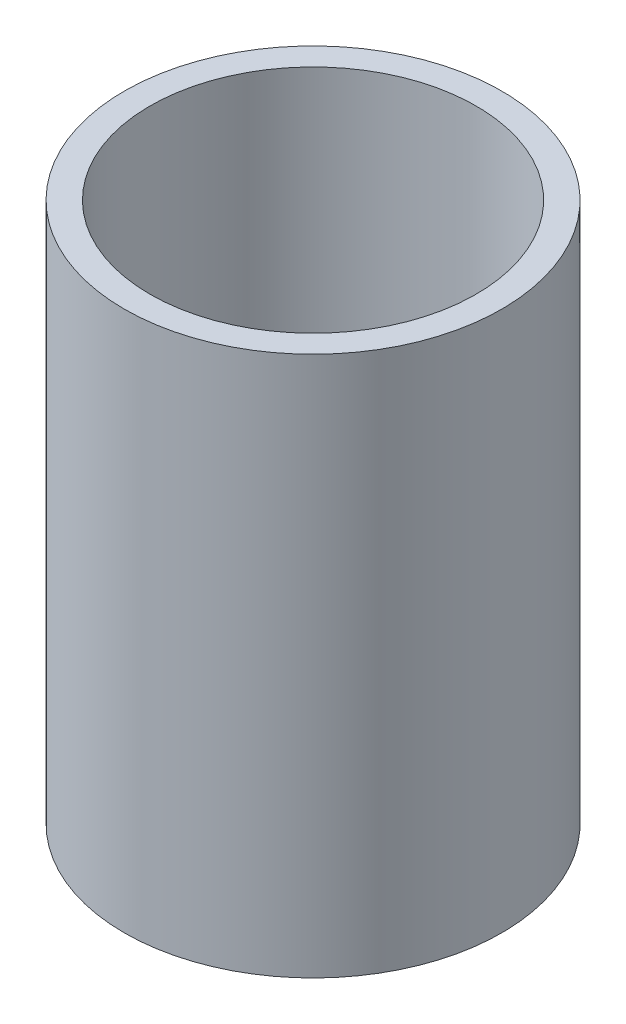
SolidWorks part; units mm, degrees
material "Corrugated Paper"
ref_plane "Front Plane" through (0, 0, 0) normal (0, 0, 1) x (1, 0, 0)
ref_plane "Top Plane" through (0, 0, 0) normal (0, 1, 0) x (1, 0, 0)
ref_plane "Right Plane" through (0, 0, 0) normal (1, 0, 0) x (0, 0, -1)
ref_axis "Axis1" through (0, 55, 0) along (0, -1, 0)
sketch "Sketch1" plane through (0, 0, 0) normal (0, 0, 1) x (1, 0, 0)
  line L1 (-46.609, 45.6176) -> (-40.259, 45.6176)
  line L2 (-46.609, 45.6176) -> (-46.609, -87.7324)
  line L3 (-46.609, -87.7324) -> (-40.259, -87.7324)
  line L4 (-40.259, 45.6176) -> (-40.259, -87.7324)
  line L5 (-38.1, 45.6176) -> (0, 45.6176) construction
  line L6 (-38.1, -87.7324) -> (0, -87.7324) construction
revolve "Revolve1" add sketch "Sketch1" angle 360 about axis through (0, 55, 0) along (0, -1, 0)
